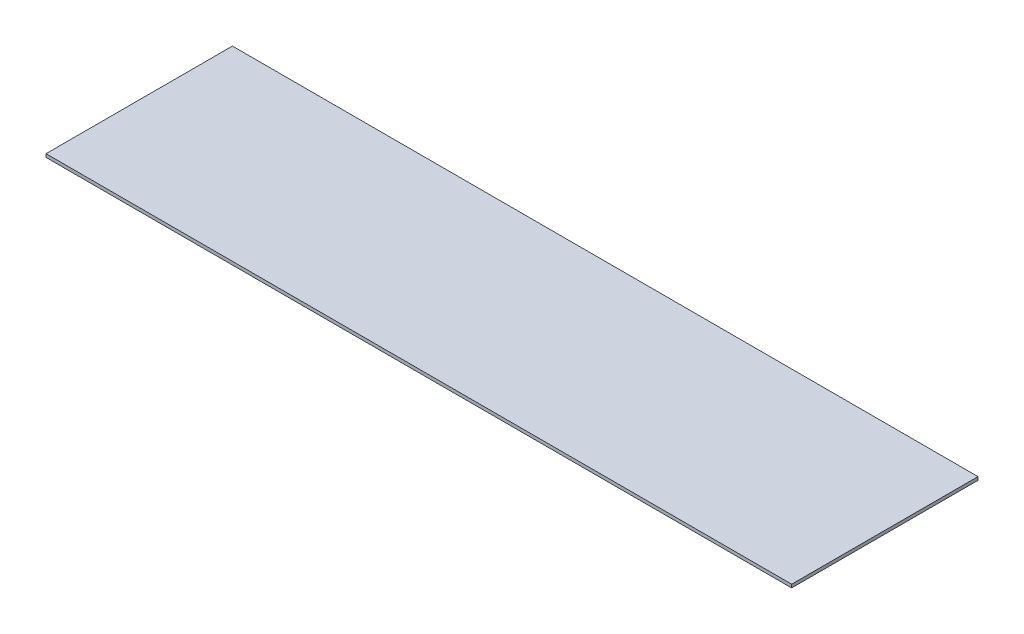
SolidWorks part; units mm, degrees
ref_plane "Front Plane" through (0, 0, 0) normal (0, 0, 1) x (1, 0, 0)
ref_plane "Top Plane" through (0, 0, 0) normal (0, 1, 0) x (1, 0, 0)
ref_plane "Right Plane" through (0, 0, 0) normal (1, 0, 0) x (0, 0, -1)
sketch "Sketch1" plane through (0, 0, 0) normal (0, 1, 0) x (1, 0, 0)
  line L1 (-3999.9999, 184.6882) -> (4000.0001, 183.9333)
  line L2 (-3999.9999, 184.6882) -> (-4000, -1815.3118)
  line L3 (-4000, -1815.3118) -> (4000, -1815.3118)
  line L4 (4000.0001, 183.9333) -> (4000, -1815.3118)
  line L5 (-3999.9999, 184.6882) -> (4000, -1815.3118) construction
  line L6 (-4000, -1815.3118) -> (4000.0001, 183.9333) construction
  point P0 (0, 0)
  dimension "D1" = 8000
  dimension "D2" = 2000
extrude "Boss-Extrude1" add sketch "Sketch1" along normal blind 35
